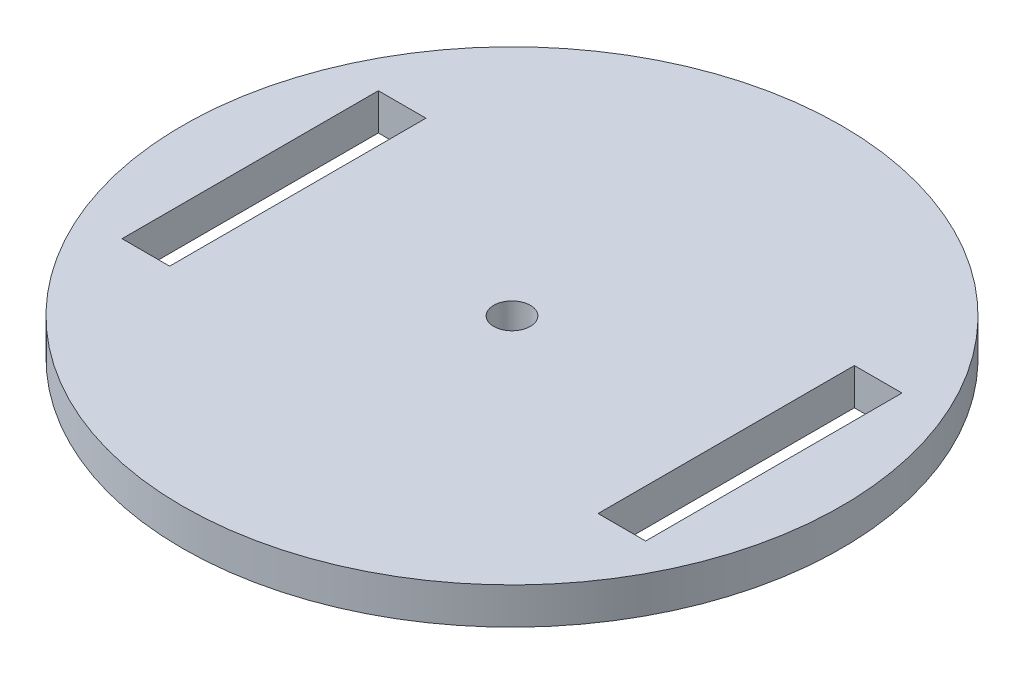
SolidWorks part; units mm, degrees
ref_plane "Front Plane" through (0, 0, 0) normal (0, 0, 1) x (1, 0, 0)
ref_plane "Top Plane" through (0, 0, 0) normal (0, 1, 0) x (1, 0, 0)
ref_plane "Right Plane" through (0, 0, 0) normal (1, 0, 0) x (0, 0, -1)
sketch "Sketch1" plane through (0, 0, 0) normal (0, 1, 0) x (1, 0, 0)
  line L0 (0, 31.7824) -> (0, -31.7824)
  line L1 (-71.5, 35) -> (-58.5, 35)
  line L2 (-71.5, 35) -> (-71.5, -35)
  line L3 (-71.5, -35) -> (-58.5, -35)
  line L4 (-58.5, 35) -> (-58.5, -35)
  line L5 (-71.5, 35) -> (-58.5, -35) construction
  line L6 (-71.5, -35) -> (-58.5, 35) construction
  line L7 (71.5, -35) -> (58.5, -35)
  line L8 (71.5, 35) -> (58.5, 35)
  line L9 (58.5, 35) -> (58.5, -35)
  line L10 (71.5, 35) -> (71.5, -35)
  circle A0 centre (0, 0) radius 90
  point P3 (-65, 0)
  point P11 (0, 0)
  dimension "D1" = 180
  dimension "D2" = 65
  dimension "D3" = 13
  dimension "D4" = 70
extrude "Boss-Extrude1" add sketch "Sketch1" along normal blind 10
sketch "Sketch2" plane through (0, 0, 0) normal (0, -1, 0) x (1, 0, 0)
  circle A0 centre (0, 0) radius 5
  dimension "D1" = 10
extrude "Cut-Extrude1" cut sketch "Sketch2" against normal up to next
